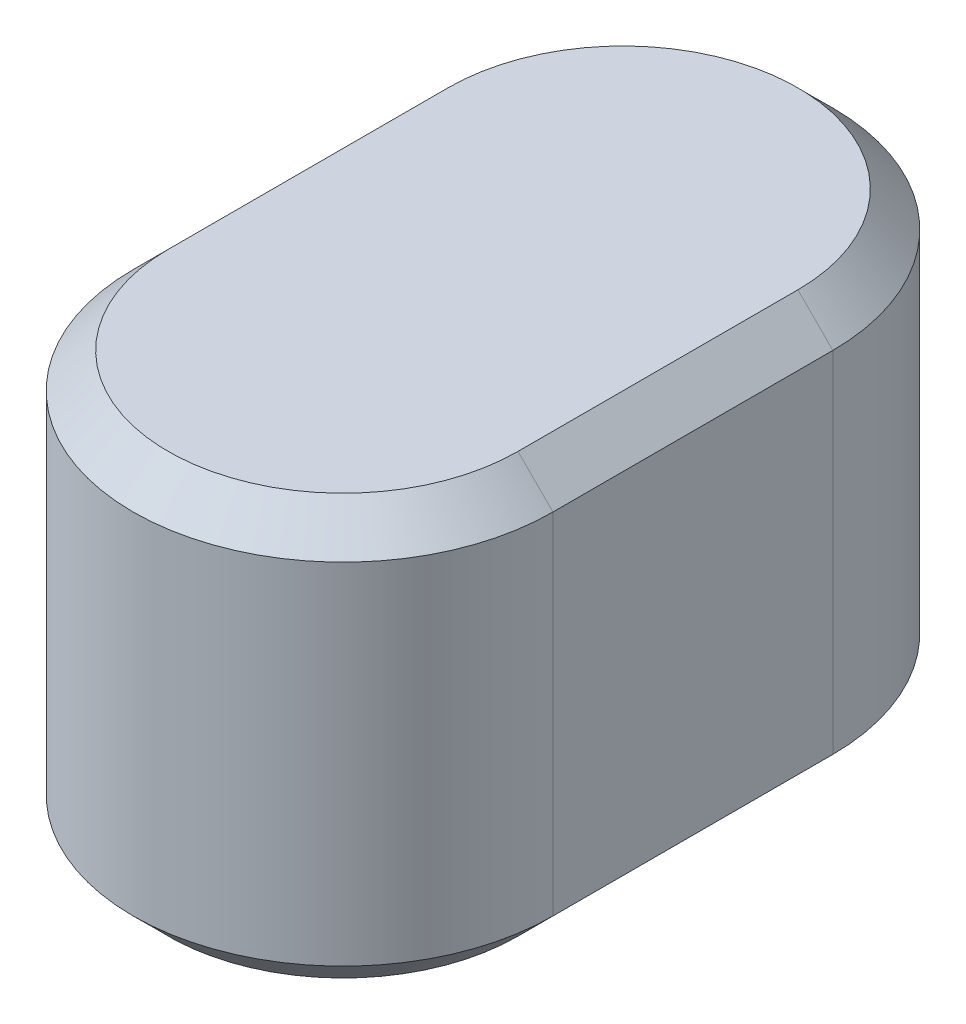
SolidWorks part; units mm, degrees
material "AISI 4340 Steel, normalized"
ref_plane "Front Plane" through (0, 0, 0) normal (0, 0, 1) x (1, 0, 0)
ref_plane "Top Plane" through (0, 0, 0) normal (0, 1, 0) x (1, 0, 0)
ref_plane "Right Plane" through (0, 0, 0) normal (1, 0, 0) x (0, 0, -1)
sketch "Sketch1" plane through (0, 0, 0) normal (0, 1, 0) x (1, 0, 0)
  line L0 (0, 0) -> (0, 8) construction
  line L1 (6, 0) -> (6, 8)
  line L2 (-6, 0) -> (-6, 8)
  arc A0 (6, 0) -> (-6, 0) centre (0, 0) cw
  arc A1 (6, 8) -> (-6, 8) centre (0, 8) ccw
  dimension "D1" = 8
  dimension "D2" = 6
  dimension "D3" = 6
extrude "Boss-Extrude1" add sketch "Sketch1" along normal blind 12
chamfer "Chamfer1" distance 1 8 edges at (-6, 0, -4) (0, 0, 6) (0, 0, -14) (6, 0, -4) (-6, 12, -4) (0, 12, 6) (0, 12, -14) (6, 12, -4)
